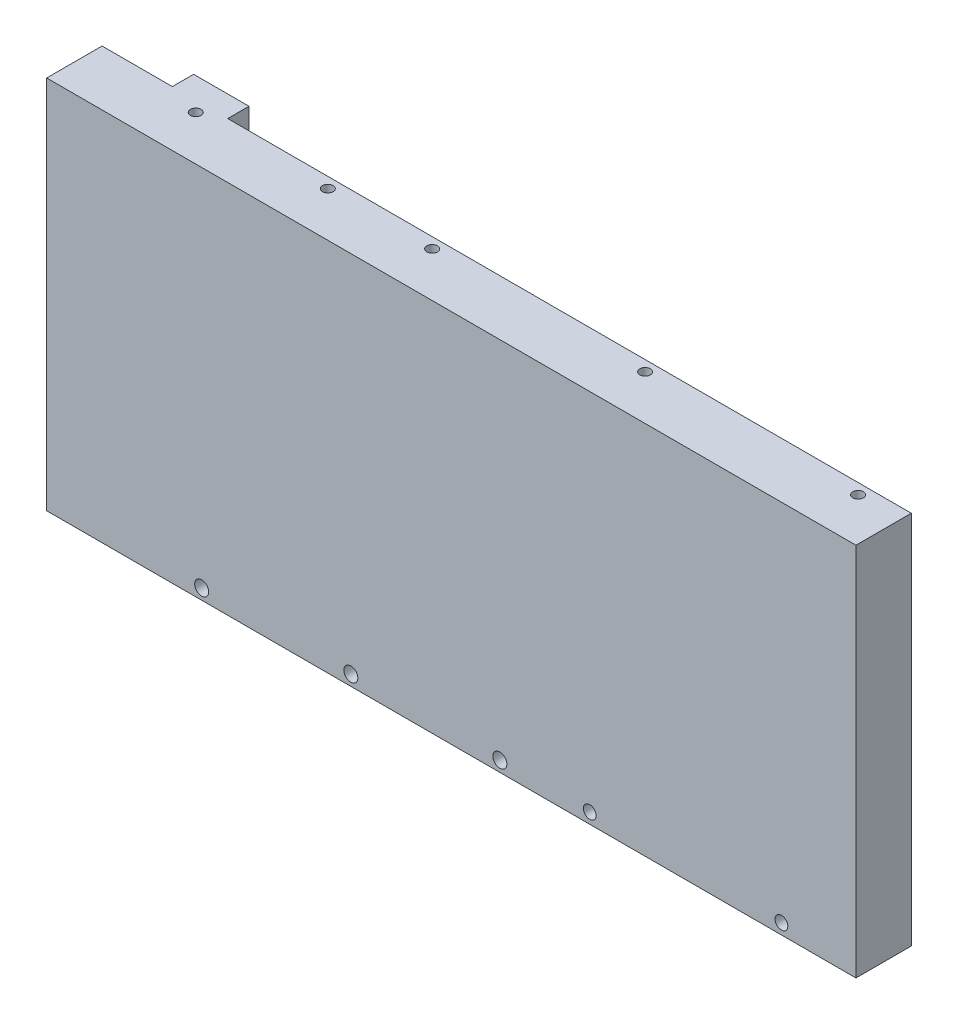
SolidWorks part; units mm, degrees
ref_plane "Front Plane" through (0, 0, 0) normal (0, 0, 1) x (1, 0, 0)
ref_plane "Top Plane" through (0, 0, 0) normal (0, 1, 0) x (1, 0, 0)
ref_plane "Right Plane" through (0, 0, 0) normal (1, 0, 0) x (0, 0, -1)
sketch "Sketch1" plane through (0, 0, 0) normal (0, 0, 1) x (1, 0, 0)
  line L0 (-95, 44) -> (-35, 44)
  line L2 (-95, 44) -> (-95, -44)
  line L3 (-95, -44) -> (95, -44)
  line L4 (95, 44) -> (95, -44)
  line L5 (-95, 44) -> (95, -44) construction
  line L7 (-35, 44) -> (95, 44)
  point P0 (0, 0)
  point P11 (0, 0)
  dimension "D1" = 130
  dimension "D2" = 88
  dimension "D3" = 190
extrude "Boss-Extrude1" add sketch "Sketch1" along normal blind 13
sketch "Sketch3" plane through (0, 0, 13) normal (0, 0, 1) x (1, 0, 0)
  line L0 (-58.6, -41.5) -> (-23.6, -41.5) construction
  line L1 (-23.6, -41.5) -> (11.4, -41.5) construction
  line L2 (32.5, -41.5) -> (77.5, -41.5) construction
  line L3 (-95, -44) -> (95, -44) construction
  line L4 (95, -44) -> (95, 44) construction
  line L5 (-95, 44) -> (-95, -44) construction
  circle A0 centre (-58.6, -41.5) radius 1.65
  circle A1 centre (-23.6, -41.5) radius 1.65
  circle A2 centre (11.4, -41.5) radius 1.65
  circle A3 centre (32.5, -41.5) radius 1.5
  circle A4 centre (77.5, -41.5) radius 1.5
  point P12 (55, -41.5)
  dimension "D1" = 3.3
  dimension "D4" = 3
  dimension "D2" = 45
  dimension "D3" = 2.5
  dimension "D5" = 40
  dimension "D6" = 2.5
  dimension "D7" = 36.4
  dimension "D8" = 35
extrude "Cut-Extrude1" cut sketch "Sketch3" against normal through all
sketch "Sketch4" plane through (0, 0, 0) normal (0, 0, -1) x (-1, 0, 0)
  line L0 (-95, 44) -> (95, 44) construction
  line L1 (65.5, 44) -> (78.5, 44)
  line L2 (65.5, 44) -> (65.5, -39)
  line L3 (65.5, -39) -> (78.5, -39)
  line L4 (78.5, 44) -> (78.5, -39)
  line L5 (95, 44) -> (95, -44) construction
  line L6 (95, -44) -> (-95, -44) construction
  dimension "D1" = 13
  dimension "D2" = 16.5
  dimension "D3" = 5
extrude "Boss-Extrude2" add sketch "Sketch4" along normal blind 5
sketch "Sketch5" plane through (0, 0, 0) normal (0, 0, -1) x (-1, 0, 0)
  line L0 (65.5, -39) -> (-15, -39)
  line L1 (-15, -39) -> (-15, -34)
  line L2 (-15, -34) -> (-14, -34)
  line L3 (-14, -34) -> (-14, -38)
  line L4 (-14, -38) -> (65.5, -38)
  line L5 (65.5, 44) -> (65.5, -39) construction
  line L6 (65.5, -38) -> (65.5, -39)
  dimension "D1" = 1
  dimension "D2" = 5
  dimension "D3" = 80.5
  dimension "D4" = 1
extrude "Boss-Extrude3" add sketch "Sketch5" along normal blind 1
fillet "Fillet1" radius 2 1 edges at (14, -38, -0.5)
sketch "草图1" plane through (0, 44, 0) normal (0, 1, 0) x (1, 0, 0)
  line L0 (-70.5, -2.5) -> (-39.5, -2.5) construction
  line L1 (-39.5, -2.5) -> (-15, -2.5) construction
  line L2 (-15, -2.5) -> (35, -2.5) construction
  line L3 (35, -2.5) -> (85, -2.5) construction
  line L5 (95, -2.5) -> (85, -2.5) construction
  line L6 (-78.5, 5) -> (-78.5, 0) construction
  line L7 (95, 0) -> (-65.5, 0) construction
  dimension "D1" = 8
  dimension "D2" = 50
  dimension "D3" = 10
  dimension "D4" = 31
  dimension "D5" = 2.5
hole_wizard "M3 螺纹孔1" positions "3D草图1" profile "草图2" tap size "M3" standard "ISO"
sketch3d "3D草图1"
  point P0 (-70.5, 44, 2.5)
  point P3 (-39.5, 44, 2.5)
  point P6 (-15, 44, 2.5)
  point P9 (35, 44, 2.5)
  point P12 (85, 44, 2.5)
sketch "草图2" plane through (-70.5, 44, 2.5) normal (1, 0, 0) x (0, 0, 1)
  line L0 (0, 0) -> (0, 12.7511)
  line L1 (0, 12.7511) -> (1.25, 12)
  line L2 (1.25, 12) -> (1.25, 0)
  line L5 (1.25, 0) -> (0, 0)
  line L10 (0, 12.7511) -> (-1.25, 12) construction
  line L11 (0, -6.35) -> (0, 107.95) construction
  dimension "螺纹孔钻头直径" = 2.5
  dimension "螺纹孔钻头深度" = 12
  dimension "导头角度" = 118
cosmetic thread "孔螺蚊线1" parameters "D1"=10, "D2"=3
cosmetic thread "孔螺蚊线2" parameters "D1"=10, "D2"=3
cosmetic thread "孔螺蚊线3" parameters "D1"=10, "D2"=3
cosmetic thread "孔螺蚊线4" parameters "D1"=10, "D2"=3
cosmetic thread "孔螺蚊线5" parameters "D1"=10, "D2"=3
sketch "草图4" plane through (0, 0, -5) normal (0, 0, -1) x (-1, 0, 0)
  line L4 (39.5, 44) -> (15, 44) construction
  line L8 (65.5, 44) -> (65.5, -39) construction
  line L9 (29.5, 29) -> (29.5, 4)
  line L10 (43.5, 4) -> (43.5, 29)
  arc A0 (29.5, 29) -> (43.5, 29) centre (36.5, 29) cw
  arc A2 (29.5, 4) -> (43.5, 4) centre (36.5, 4) ccw
  dimension "D1" = 7
  dimension "D3" = 29
  dimension "D2" = 15
  dimension "D4" = 25
extrude "切除-拉伸1" cut sketch "草图4" against normal blind 17
